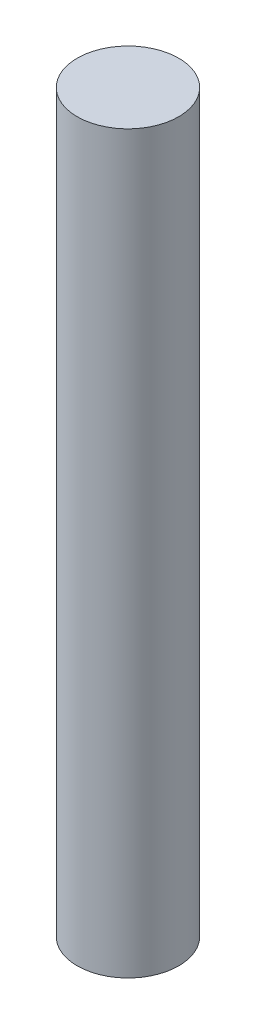
SolidWorks part; units mm, degrees
material "Stainless Steel (ferritic)"
ref_plane "Front Plane" through (0, 0, 0) normal (0, 0, 1) x (1, 0, 0)
ref_plane "Top Plane" through (0, 0, 0) normal (0, 1, 0) x (1, 0, 0)
ref_plane "Right Plane" through (0, 0, 0) normal (1, 0, 0) x (0, 0, -1)
sketch "Sketch1" plane through (0, 0, 0) normal (0, 1, 0) x (1, 0, 0)
  circle A0 centre (0, 0) radius 1.7526
  dimension "D1" = 3.5052
extrude "Boss-Extrude1" add sketch "Sketch1" along normal blind 25.4
